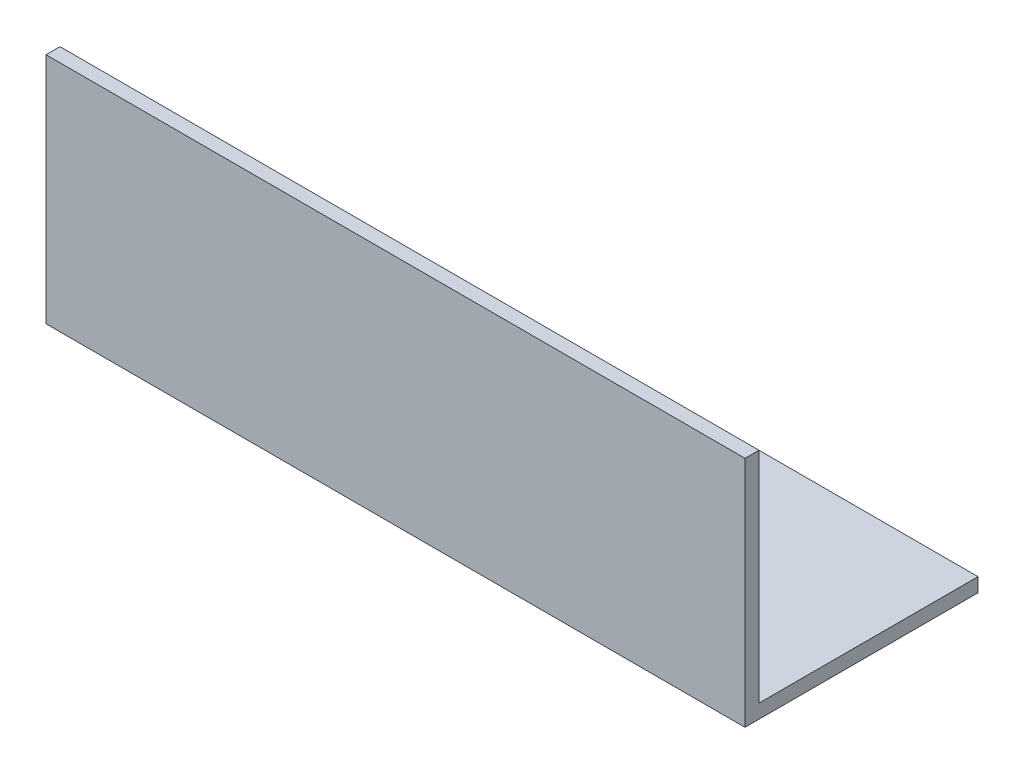
SolidWorks part; units mm, degrees
material "Plain Carbon Steel"
ref_plane "Front Plane" through (0, 0, 0) normal (0, 0, 1) x (1, 0, 0)
ref_plane "Top Plane" through (0, 0, 0) normal (0, 1, 0) x (1, 0, 0)
ref_plane "Right Plane" through (0, 0, 0) normal (1, 0, 0) x (0, 0, -1)
sketch "Sketch1" plane through (0, 0, 0) normal (1, 0, 0) x (0, 0, -1)
  line L1 (0, 0) -> (25.4, 0)
  line L2 (0, 0) -> (0, 25.4)
  dimension "D1" = 25.4
  dimension "D2" = 25.4
extrude "Extrude-Thin1" add sketch "Sketch1" along normal blind 76.2 thin thin type one direction reverse wall 1.524
